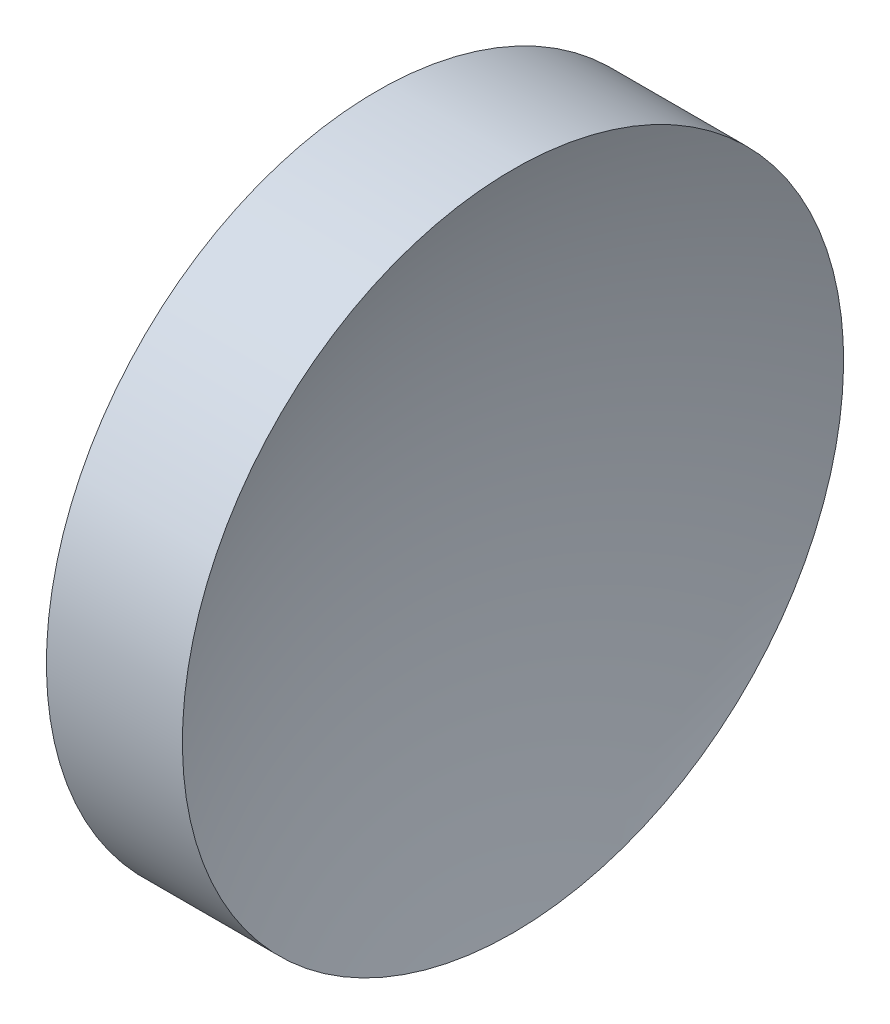
SolidWorks part; units mm, degrees
ref_plane "前视基准面" through (0, 0, 0) normal (0, 0, 1) x (1, 0, 0)
ref_plane "上视基准面" through (0, 0, 0) normal (0, 1, 0) x (1, 0, 0)
ref_plane "右视基准面" through (0, 0, 0) normal (1, 0, 0) x (0, 0, -1)
sketch "草图1" plane through (0, 0, 0) normal (0, 0, 1) x (1, 0, 0)
  line L0 (44.7048, 26.0233) -> (53.254, 26.0233) construction
  line L1 (46.5855, 26.0233) -> (46.5855, 36.0233)
  line L2 (46.5855, 36.0233) -> (50.6989, 36.0233)
  line L3 (48.6855, 26.0233) -> (46.5855, 26.0233)
  arc A0 (50.6989, 36.0233) -> (48.6855, 26.0233) centre (74.5255, 26.0233) ccw
  dimension "D3" = 25.84
  dimension "D1" = 10
  dimension "D2" = 4.1134
revolve "旋转1" add sketch "草图1" angle 360 about L0
